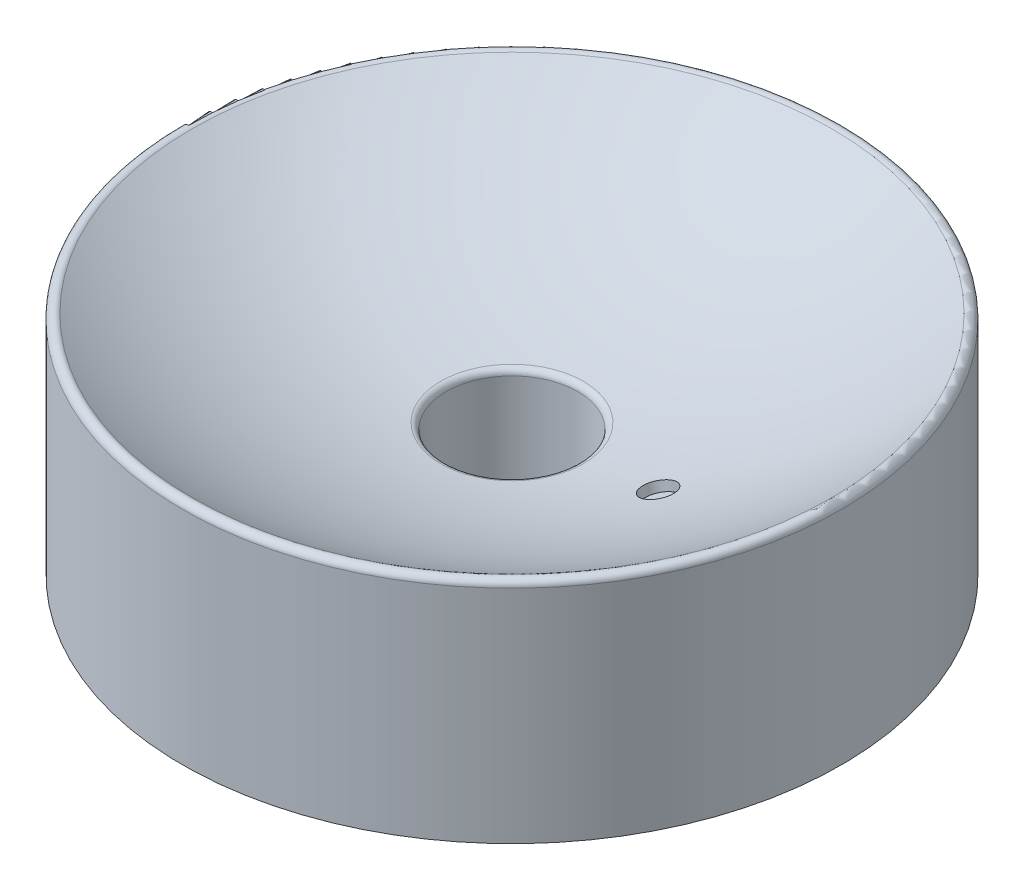
SolidWorks part; units mm, degrees
ref_plane "Ebene vorne" through (0, 0, 0) normal (0, 0, 1) x (1, 0, 0)
ref_plane "Ebene oben" through (0, 0, 0) normal (0, 1, 0) x (1, 0, 0)
ref_plane "Ebene rechts" through (0, 0, 0) normal (1, 0, 0) x (0, 0, -1)
sketch "Skizze1" plane through (0, 0, 0) normal (0, 0, 1) x (1, 0, 0)
  line L0 (0, 0) -> (0, 31.0212) construction
  line L1 (21, 40) -> (21, 0)
  line L2 (105, 70.4909) -> (105, 0)
  line L3 (21, 0) -> (22.5, 0)
  line L4 (103.5, 0) -> (103.5, 59.374)
  line L5 (105, 0) -> (103.5, 0)
  line L6 (22.5, 0) -> (22.5, 30.992)
  arc A0 (22.7473, 41.984) -> (101.8681, 72.1398) centre (0, 220.5409) ccw
  arc A1 (23.377, 31.9844) -> (101.9634, 60.2178) centre (0, 220.5409) ccw
  arc A2 (26.6, 32.4121) -> (139.3333, 91.3657) centre (0, 220.5409) ccw construction
  arc A3 (25.2, 42.3136) -> (132, 98.1644) centre (0, 220.5409) ccw construction
  arc A4 (101.8681, 72.1398) -> (105, 70.4909) centre (103, 70.4909) cw
  arc A5 (21, 40) -> (22.7473, 41.984) centre (23, 40) cw
  arc A6 (103.5, 59.374) -> (101.9634, 60.2178) centre (102.5, 59.374) ccw
  arc A7 (22.5, 30.992) -> (23.377, 31.9844) centre (23.5, 30.992) cw
  dimension "D3" = 180
  dimension "D2" = 2
  dimension "D4" = 1
  dimension "D1" = 10
  dimension "D5" = 40
  dimension "D6" = 42
  dimension "D7" = 210
  dimension "D8" = 1.5
revolve "Rotation1" add sketch "Skizze1" angle 360 about L0
sketch "Skizze3" plane through (0, 0, 0) normal (0, 0, 1) x (1, 0, 0)
  line L0 (41.7398, 45.4472) -> (42.5163, 42.5494)
  line L1 (0, 220.5409) -> (63.6384, -16.961) construction
  line L2 (42.5163, 42.5494) -> (45.897, 43.4553)
  line L3 (45.897, 43.4553) -> (48.2264, 34.762)
  line L4 (48.2264, 34.762) -> (49.6753, 35.1502)
  line L5 (49.6753, 35.1502) -> (46.5695, 46.7413)
  line L6 (46.5695, 46.7413) -> (41.7398, 45.4472)
  line L7 (0, 0) -> (0, 31.0212) construction
  arc A0 (22.7473, 41.984) -> (101.8681, 72.1398) centre (0, 220.5409) ccw construction
  arc A1 (22.7473, 41.984) -> (101.8681, 72.1398) centre (0, 220.5409) ccw construction
  point P1 (48.572, 47.2181)
  dimension "D1" = 10
  dimension "D2" = 3
  dimension "D3" = 3
  dimension "D4" = 15
  dimension "D5" = 12
revolve "Schnitt-Rotation1" cut sketch "Skizze3" angle 360 about L1
